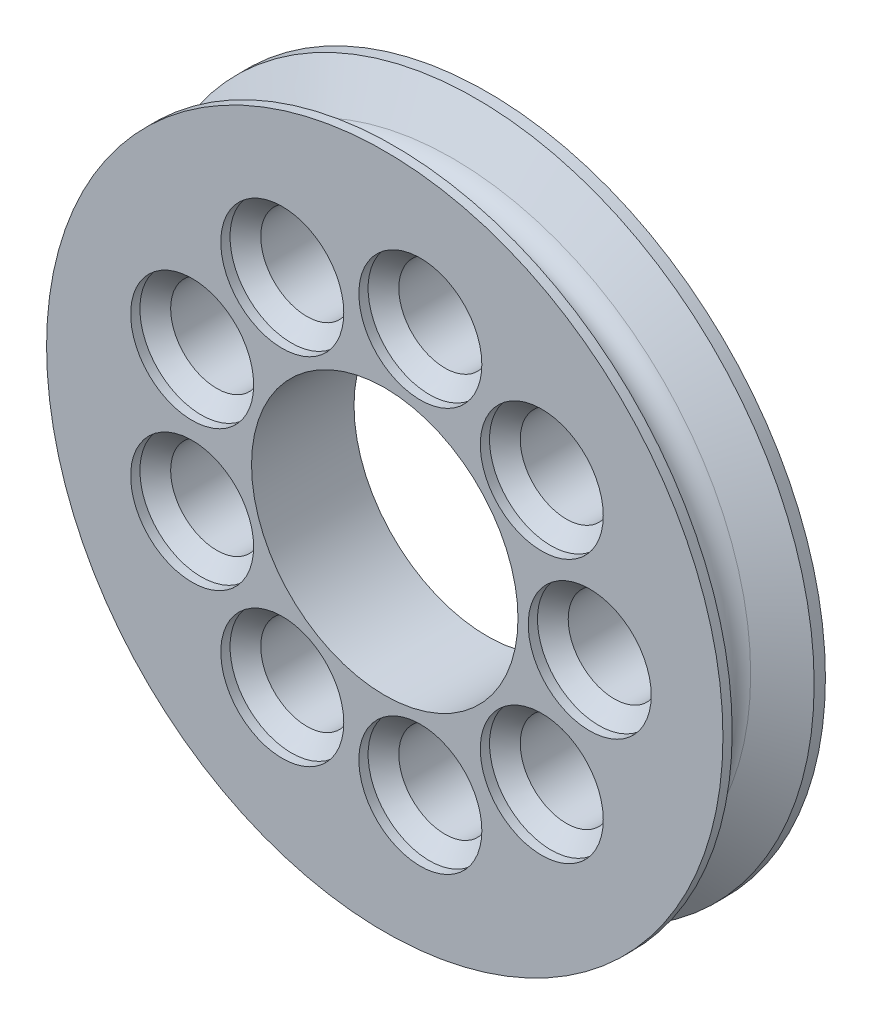
SolidWorks part; units mm, degrees
ref_plane "Front Plane" through (0, 0, 0) normal (0, 0, 1) x (1, 0, 0)
ref_plane "Top Plane" through (0, 0, 0) normal (0, 1, 0) x (1, 0, 0)
ref_plane "Right Plane" through (0, 0, 0) normal (1, 0, 0) x (0, 0, -1)
sketch "Sketch1" plane through (0, 0, 0) normal (0, 1, 0) x (1, 0, 0)
  line L0 (0, 0) -> (4.9888, 2.8803)
  line L5 (0, 0) -> (16.51, 0) construction
  line L7 (0, 10.16) -> (16.526, 10.16) construction
  line L9 (0, 10.16) -> (4.9888, 7.2797)
  line L10 (0, 11.5553) -> (0, 10.16)
  line L11 (0, -1.1447) -> (41.91, -1.1447)
  line L15 (0, 0) -> (0, -1.1447)
  line L16 (4.9888, 7.2797) -> (16.51, 7.2797) construction
  line L17 (4.9888, 2.8803) -> (16.51, 2.8803) construction
  line L18 (0, 11.5553) -> (41.91, 11.5553)
  line L19 (41.91, 11.5553) -> (41.91, -1.1447)
  arc A0 (4.9888, 7.2797) -> (4.9888, 2.8803) centre (3.7188, 5.08) cw
  point P6 (8.7988, 5.08)
  dimension "D5" = 2.54
  dimension "D1" = 10.16
  dimension "D2" = 16.526
  dimension "D3" = 10.16
  dimension "D4" = 10.16
  dimension "D6" = 12.7
  dimension "D7" = 41.91
  dimension "D8" = 11.5212
  dimension "D9" = 41.91
  dimension "D10" = 1.1447
revolve "Revolve1" add sketch "Sketch1" angle 360 about L19
sketch "Sketch2" plane through (0, 0, 0) normal (0, 0, 1) x (1, 0, 0)
  line L0 (41.91, 41.91) -> (41.91, -41.91) construction
  line L1 (0, 0) -> (83.82, 0) construction
  line L2 (18.0418, 8.6873) -> (29.21, 21.997) construction
  line L3 (29.21, 21.997) -> (46.3207, 25.0141) construction
  line L4 (46.3207, 25.0141) -> (61.3675, 16.3268) construction
  line L5 (61.3675, 16.3268) -> (67.31, 0) construction
  line L6 (67.31, 0) -> (61.3675, -16.3268) construction
  line L7 (61.3675, -16.3268) -> (46.3207, -25.0141) construction
  line L8 (46.3207, -25.0141) -> (29.21, -21.997) construction
  line L9 (29.21, -21.997) -> (18.0418, -8.6873) construction
  line L10 (18.0418, -8.6873) -> (18.0418, 8.6873) construction
  circle A0 centre (41.91, 0) radius 41.91 construction
  circle A1 centre (41.91, 0) radius 16.51 construction
  circle A2 centre (41.91, 0) radius 25.4 construction
  circle A3 centre (67.31, 0) radius 7.62
  circle A4 centre (61.3675, -16.3268) radius 7.62
  circle A5 centre (61.3675, 16.3268) radius 7.62
  circle A6 centre (46.3207, 25.0141) radius 7.62
  circle A7 centre (29.21, 21.997) radius 7.62
  circle A8 centre (18.0418, 8.6873) radius 7.62
  circle A9 centre (18.0418, -8.6873) radius 7.62
  circle A10 centre (29.21, -21.997) radius 7.62
  circle A11 centre (46.3207, -25.0141) radius 7.62
  dimension "D1" = 33.02
  dimension "D2" = 50.8
  dimension "D3" = 15.24
sketch "Sketch4" plane through (0, 0, 0) normal (0, 0, 1) x (1, 0, 0)
  line L0 (0, 0) -> (83.82, 0) construction
  line L1 (29.21, 21.997) -> (46.3207, 25.0141) construction
  line L2 (46.3207, 25.0141) -> (61.3675, 16.3268) construction
  line L3 (61.3675, 16.3268) -> (67.31, 0) construction
  line L4 (67.31, 0) -> (61.3675, -16.3268) construction
  line L5 (61.3675, -16.3268) -> (46.3207, -25.0141) construction
  line L6 (46.3207, -25.0141) -> (29.21, -21.997) construction
  line L7 (29.21, -21.997) -> (18.0418, -8.6873) construction
  line L8 (18.0418, -8.6873) -> (18.0418, 8.6873) construction
  line L9 (18.0418, 8.6873) -> (29.21, 21.997) construction
  circle A0 centre (67.31, 0) radius 5.715
  circle A1 centre (41.91, 0) radius 25.4 construction
  circle A2 centre (61.3675, 16.3268) radius 5.715
  circle A3 centre (46.3207, 25.0141) radius 5.715
  circle A4 centre (29.21, 21.997) radius 5.715
  circle A5 centre (18.0418, 8.6873) radius 5.715
  circle A6 centre (18.0418, -8.6873) radius 5.715
  circle A7 centre (29.21, -21.997) radius 5.715
  circle A8 centre (46.3207, -25.0141) radius 5.715
  circle A9 centre (61.3675, -16.3268) radius 5.715
  circle A10 centre (18.0418, 8.6873) radius 7.62 construction
  circle A11 centre (29.21, 21.997) radius 7.62 construction
  circle A12 centre (46.3207, 25.0141) radius 7.62 construction
  circle A13 centre (61.3675, 16.3268) radius 7.62 construction
  circle A14 centre (67.31, 0) radius 7.62 construction
  circle A15 centre (61.3675, -16.3268) radius 7.62 construction
  circle A16 centre (46.3207, -25.0141) radius 7.62 construction
  circle A17 centre (29.21, -21.997) radius 7.62 construction
  circle A18 centre (18.0418, -8.6873) radius 7.62 construction
  point P22 (0, 0)
  dimension "D1" = 11.43
  dimension "D2" = 15.24
sketch "Sketch5" plane through (0, 0, 1.1447) normal (0, 0, 1) x (1, 0, 0)
  circle A0 centre (41.91, 0) radius 16.51
extrude "Cut-Extrude2" cut sketch "Sketch5" against normal blind 110.744 and the other way blind 19.304
sketch "Sketch6" plane through (0, 0, 0) normal (0, 0, 1) x (1, 0, 0)
extrude "Cut-Extrude3" cut sketch "Sketch2" against normal blind 1.905 draft 45 and the other way blind 9.398
sketch "Sketch7" plane through (0, 0, 0) normal (0, 0, 1) x (1, 0, 0)
  circle A0 centre (61.3675, 16.3268) radius 7.62
  circle A1 centre (46.3207, 25.0141) radius 7.62
  circle A2 centre (29.21, 21.997) radius 7.62
  circle A3 centre (18.0418, 8.6873) radius 7.62
  circle A4 centre (18.0418, -8.6873) radius 7.62
  circle A5 centre (29.21, -21.997) radius 7.62
  circle A6 centre (46.3207, -25.0141) radius 7.62
  circle A7 centre (61.3675, -16.3268) radius 7.62
  circle A8 centre (67.31, 0) radius 7.62
  dimension "D1" = 15.24
ref_plane "Plane1" through (0, 0, -14.0953) normal (0, 0, -1) x (-1, 0, 0)
sketch "Sketch8" plane through (0, 0, -14.0953) normal (0, 0, -1) x (-1, 0, 0)
  circle A0 centre (-61.3675, 16.3268) radius 8.2136
  circle A1 centre (-46.3207, 25.0141) radius 7.62
  circle A2 centre (-29.21, 21.997) radius 7.62
  circle A3 centre (-18.0418, 8.6873) radius 7.3669
  point P12 (0, 0)
ref_plane "Plane2" through (0, 0, -11.5553) normal (0, 0, -1) x (-1, 0, 0)
sketch "Sketch9" plane through (0, 0, -11.5553) normal (0, 0, -1) x (-1, 0, 0)
  circle A0 centre (-67.31, 0) radius 7.62
  circle A1 centre (-61.3675, 16.3268) radius 7.62
  circle A2 centre (-46.3207, 25.0141) radius 7.62
  circle A3 centre (-29.21, 21.997) radius 7.62
  circle A4 centre (-18.0418, 8.6873) radius 7.62
  circle A5 centre (-18.0418, -8.6873) radius 7.62
  circle A6 centre (-29.21, -21.997) radius 7.62
  circle A7 centre (-46.3207, -25.0141) radius 7.62
  circle A8 centre (-61.3675, -16.3268) radius 7.62
  dimension "D1" = 15.24
extrude "Cut-Extrude5" cut sketch "Sketch9" against normal blind 1.905 draft 45 and the other way blind 127
ref_plane "Plane3" through (0, 0, 1.1447) normal (0, 0, 1) x (1, 0, 0)
sketch "Sketch10" plane through (0, 0, 1.1447) normal (0, 0, 1) x (1, 0, 0)
  circle A0 centre (29.21, 21.997) radius 5.715
  circle A1 centre (46.3207, 25.0141) radius 5.715
  circle A2 centre (61.3675, 16.3268) radius 5.715
  circle A3 centre (67.31, 0) radius 5.715
  circle A4 centre (61.3675, -16.3268) radius 5.715
  circle A5 centre (46.3207, -25.0141) radius 5.715
  circle A6 centre (29.21, -21.997) radius 5.715
  circle A7 centre (18.0418, -8.6873) radius 5.715
  circle A8 centre (18.0418, 8.6873) radius 5.715
  dimension "D1" = 11.43
extrude "Cut-Extrude6" cut sketch "Sketch10" against normal blind 48.641 and the other way blind 1.905
